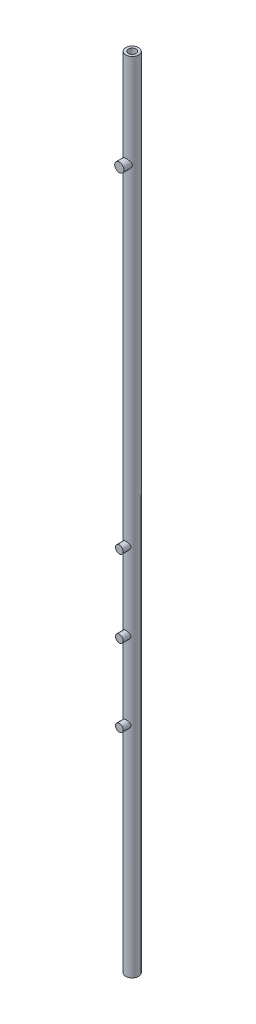
SolidWorks part; units mm, degrees
ref_plane "Front Plane" through (0, 0, 0) normal (0, 0, 1) x (1, 0, 0)
ref_plane "Top Plane" through (0, 0, 0) normal (0, 1, 0) x (1, 0, 0)
ref_plane "Right Plane" through (0, 0, 0) normal (1, 0, 0) x (0, 0, -1)
sketch "Sketch1" plane through (0, 0, 0) normal (0, 1, 0) x (1, 0, 0)
  circle A0 centre (0, 0) radius 2.5
  circle A1 centre (0, 0) radius 1.5
  dimension "D1" = 5
  dimension "D2" = 3
extrude "Boss-Extrude1" add sketch "Sketch1" along normal blind 310 contours A0
sketch "Sketch2" plane through (0, 0, 0) normal (0, 0, 1) x (1, 0, 0)
  circle A0 centre (0, 84.9141) radius 1.5038
extrude "Boss-Extrude2" add sketch "Sketch2" along normal blind 5
pattern_linear "LPattern1" count 3 spacing 30 along (0, 1, 0) of "Boss-Extrude2"
sketch "Sketch3" plane through (0, 0, 0) normal (0, 0, 1) x (1, 0, 0)
  circle A0 centre (0, 273.4508) radius 1.7911
extrude "Boss-Extrude3" add sketch "Sketch3" along normal blind 5
